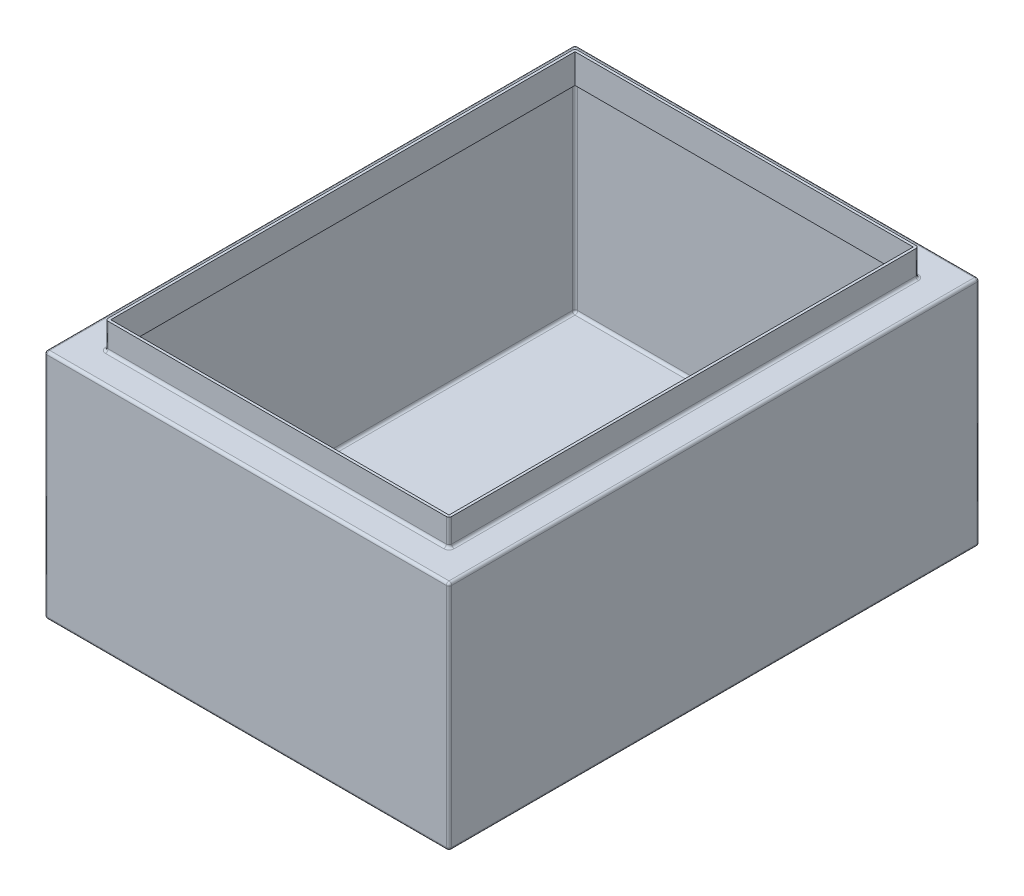
SolidWorks part; units mm, degrees
ref_plane "Front Plane" through (0, 0, 0) normal (0, 0, 1) x (1, 0, 0)
ref_plane "Top Plane" through (0, 0, 0) normal (0, 1, 0) x (1, 0, 0)
ref_plane "Right Plane" through (0, 0, 0) normal (1, 0, 0) x (0, 0, -1)
sketch "Sketch1" plane through (0, 0, 0) normal (0, 1, 0) x (1, 0, 0)
  line L1 (0, 0) -> (305, 0)
  line L2 (0, 0) -> (0, 400)
  line L3 (0, 400) -> (305, 400)
  line L4 (305, 0) -> (305, 400)
  dimension "D1" = 400
  dimension "D2" = 305
extrude "Boss-Extrude1" add sketch "Sketch1" along normal blind 175
shell "Shell1" thickness 2
sketch "Sketch2" plane through (0, 175, 0) normal (0, 1, 0) x (1, 0, 0)
  line L0 (305, 400) -> (0, 400) construction
  line L1 (25, 375) -> (280, 375)
  line L2 (25, 375) -> (25, 25)
  line L3 (25, 25) -> (280, 25)
  line L4 (280, 375) -> (280, 25)
  line L5 (305, 0) -> (305, 400) construction
  line L6 (0, 0) -> (305, 0) construction
  line L7 (0, 400) -> (0, 0) construction
  dimension "D1" = 25
  dimension "D2" = 25
  dimension "D3" = 25
  dimension "D4" = 25
extrude "Cut-Extrude1" cut sketch "Sketch2" against normal blind 5 contours L1 L4 L3 L2
sketch "Sketch3" plane through (0, 175, 0) normal (0, 1, 0) x (1, 0, 0)
  line L1 (23, 377) -> (282, 377)
  line L2 (23, 377) -> (23, 23)
  line L3 (23, 23) -> (282, 23)
  line L4 (282, 377) -> (282, 23)
  line L5 (25, 375) -> (280, 375)
  line L6 (25, 375) -> (25, 25)
  line L7 (25, 25) -> (280, 25)
  line L8 (280, 375) -> (280, 25)
  dimension "D1" = 2
  dimension "D2" = 2
  dimension "D3" = 2
  dimension "D4" = 2
extrude "Boss-Extrude2" add sketch "Sketch3" along normal blind 20
fillet "Fillet1" radius 2 32 edges at (152.5, 173, -2) (152.5, 173, -398) (2, 87.5, -2) (2, 173, -200) (2, 87.5, -398) (303, 87.5, -398) (303, 173, -200) (303, 87.5, -2) (152.5, 2, -398) (303, 2, -200) (152.5, 2, -2) (2, 2, -200) (152.5, 175, -23) (282, 185, -23) (282, 175, -200) (23, 185, -23) (23, 175, -200) (282, 185, -377) (23, 185, -377) (152.5, 175, -377) (152.5, 175, 0) (152.5, 0, 0) (305, 87.5, 0) (305, 175, -200) (305, 0, -200) (0, 175, -200) (0, 87.5, 0) (0, 0, -200) (305, 87.5, -400) (152.5, 175, -400) (0, 87.5, -400) (152.5, 0, -400)
